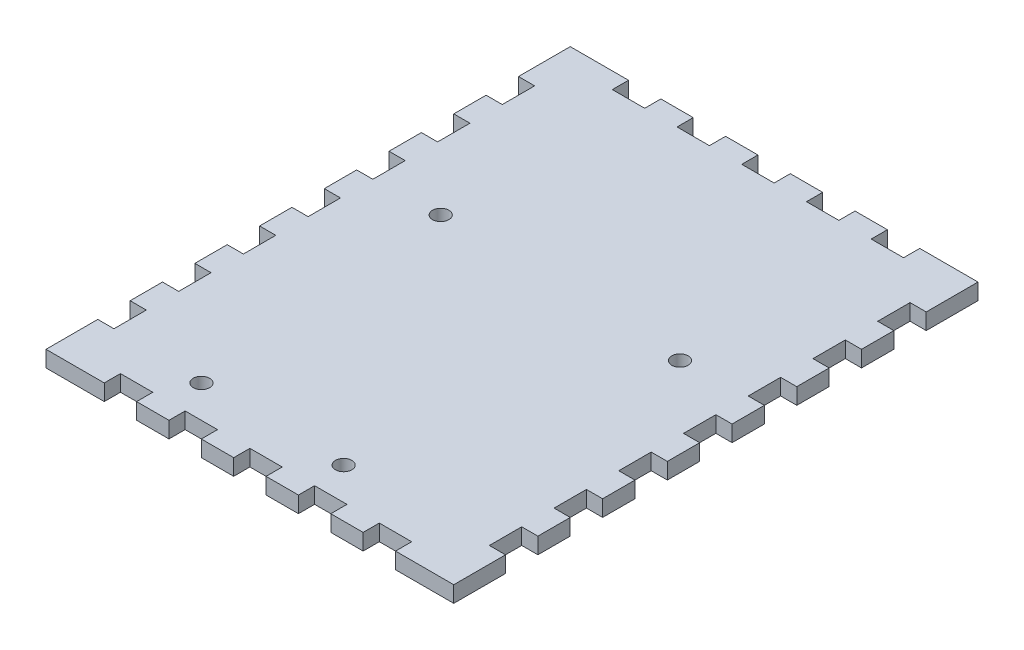
SolidWorks part; units mm, degrees
material "Acrylic (Medium-high impact)"
ref_plane "Front Plane" through (0, 0, 0) normal (0, 0, 1) x (1, 0, 0)
ref_plane "Top Plane" through (0, 0, 0) normal (0, 1, 0) x (1, 0, 0)
ref_plane "Right Plane" through (0, 0, 0) normal (1, 0, 0) x (0, 0, -1)
sketch "Sketch1" plane through (0, 0, 0) normal (0, 1, 0) x (1, 0, 0)
  line L1 (-40.005, 51.435) -> (40.005, 51.435)
  line L2 (-40.005, 51.435) -> (-40.005, -51.435)
  line L3 (-40.005, -51.435) -> (40.005, -51.435)
  line L4 (40.005, 51.435) -> (40.005, -51.435)
  line L5 (-40.005, 51.435) -> (40.005, -51.435) construction
  line L6 (-40.005, -51.435) -> (40.005, 51.435) construction
  point P0 (0, 0)
  dimension "D1" = 102.87
  dimension "D2" = 80.01
extrude "Boss-Extrude1" add sketch "Sketch1" along normal blind 3.175
sketch "Sketch2" plane through (0, 3.175, 0) normal (0, 1, 0) x (1, 0, 0)
  line L0 (-40.005, -41.275) -> (-36.83, -41.275)
  line L1 (-40.005, 51.435) -> (-40.005, -51.435) construction
  line L2 (-36.83, -41.275) -> (-36.83, -34.925)
  line L3 (-36.83, -34.925) -> (-40.005, -34.925)
  line L4 (-40.005, -51.435) -> (40.005, -51.435) construction
  line L5 (-40.005, -28.575) -> (-36.83, -28.575)
  line L6 (-40.005, 51.435) -> (-40.005, -51.435) construction
  line L7 (-36.83, -28.575) -> (-36.83, -22.225)
  line L8 (-36.83, -22.225) -> (-40.005, -22.225)
  line L9 (-40.005, -15.875) -> (-36.83, -15.875)
  line L10 (-36.83, -15.875) -> (-36.83, -9.525)
  line L11 (-36.83, -9.525) -> (-40.005, -9.525)
  line L12 (-40.005, -3.175) -> (-36.83, -3.175)
  line L13 (-36.83, -3.175) -> (-36.83, 3.175)
  line L14 (-36.83, 3.175) -> (-40.005, 3.175)
  line L15 (-40.005, 9.525) -> (-36.83, 9.525)
  line L16 (-36.83, 9.525) -> (-36.83, 15.875)
  line L17 (-36.83, 15.875) -> (-40.005, 15.875)
  line L18 (-40.005, 22.225) -> (-36.83, 22.225)
  line L19 (-36.83, 22.225) -> (-36.83, 28.575)
  line L20 (-36.83, 28.575) -> (-40.005, 28.575)
  line L21 (40.005, 51.435) -> (-40.005, 51.435) construction
  line L22 (-40.005, 51.435) -> (-40.005, -51.435) construction
  line L23 (-40.005, -34.925) -> (-40.005, -41.275)
  line L24 (-40.005, -22.225) -> (-40.005, -28.575)
  line L25 (-40.005, -9.525) -> (-40.005, -15.875)
  line L26 (-40.005, -3.175) -> (-40.005, 3.175)
  line L27 (-40.005, 15.875) -> (-40.005, 9.525)
  line L28 (-40.005, 28.575) -> (-40.005, 22.225)
  line L29 (0, 51.435) -> (0, -51.435) construction
  line L30 (40.005, 28.575) -> (40.005, 22.225)
  line L31 (40.005, 15.875) -> (40.005, 9.525)
  line L32 (40.005, -3.175) -> (40.005, 3.175)
  line L33 (40.005, -9.525) -> (40.005, -15.875)
  line L34 (40.005, -22.225) -> (40.005, -28.575)
  line L35 (40.005, -34.925) -> (40.005, -41.275)
  line L36 (36.83, 28.575) -> (40.005, 28.575)
  line L37 (36.83, 22.225) -> (36.83, 28.575)
  line L38 (40.005, 22.225) -> (36.83, 22.225)
  line L39 (36.83, 15.875) -> (40.005, 15.875)
  line L40 (36.83, 9.525) -> (36.83, 15.875)
  line L41 (40.005, 9.525) -> (36.83, 9.525)
  line L42 (36.83, 3.175) -> (40.005, 3.175)
  line L43 (36.83, -3.175) -> (36.83, 3.175)
  line L44 (40.005, -3.175) -> (36.83, -3.175)
  line L45 (36.83, -9.525) -> (40.005, -9.525)
  line L46 (36.83, -15.875) -> (36.83, -9.525)
  line L47 (40.005, -15.875) -> (36.83, -15.875)
  line L48 (36.83, -22.225) -> (40.005, -22.225)
  line L49 (36.83, -28.575) -> (36.83, -22.225)
  line L50 (40.005, -28.575) -> (36.83, -28.575)
  line L51 (36.83, -34.925) -> (40.005, -34.925)
  line L52 (36.83, -41.275) -> (36.83, -34.925)
  line L53 (40.005, -41.275) -> (36.83, -41.275)
  line L54 (-40.005, 34.925) -> (-36.83, 34.925)
  line L55 (-36.83, 34.925) -> (-36.83, 41.275)
  line L56 (-36.83, 41.275) -> (-40.005, 41.275)
  line L57 (-40.005, 41.275) -> (-40.005, 34.925)
  line L58 (40.005, 41.275) -> (40.005, 34.925)
  line L59 (36.83, 41.275) -> (40.005, 41.275)
  line L60 (36.83, 34.925) -> (36.83, 41.275)
  line L61 (40.005, 34.925) -> (36.83, 34.925)
  dimension "D1" = 3.175
  dimension "D2" = 6.35
  dimension "D3" = 10.16
  dimension "D4" = 6.35
  dimension "D5" = 6.35
  dimension "D6" = 6.35
  dimension "D7" = 6.35
  dimension "D8" = 6.35
  dimension "D9" = 10.16
  dimension "D10" = 6.35
extrude "Cut-Extrude1" cut sketch "Sketch2" against normal through all
sketch "Sketch3" plane through (0, 3.175, 0) normal (0, 1, 0) x (1, 0, 0)
  line L0 (28.575, 51.435) -> (28.575, 48.26)
  line L1 (40.005, 51.435) -> (-40.005, 51.435) construction
  line L2 (28.575, 48.26) -> (22.225, 48.26)
  line L3 (22.225, 48.26) -> (22.225, 51.435)
  line L4 (22.225, 51.435) -> (28.575, 51.435)
  line L5 (15.875, 51.435) -> (15.875, 48.26)
  line L6 (15.875, 48.26) -> (9.525, 48.26)
  line L7 (9.525, 48.26) -> (9.525, 51.435)
  line L8 (9.525, 51.435) -> (15.875, 51.435)
  line L9 (3.175, 51.435) -> (3.175, 48.26)
  line L10 (3.175, 48.26) -> (-3.175, 48.26)
  line L11 (-3.175, 48.26) -> (-3.175, 51.435)
  line L12 (-3.175, 51.435) -> (3.175, 51.435)
  line L13 (-9.525, 51.435) -> (-9.525, 48.26)
  line L14 (-9.525, 48.26) -> (-15.875, 48.26)
  line L15 (-15.875, 48.26) -> (-15.875, 51.435)
  line L16 (-15.875, 51.435) -> (-9.525, 51.435)
  line L17 (-40.005, 51.435) -> (-40.005, 41.275) construction
  line L18 (-36.83, 0) -> (36.83, 0) construction
  line L21 (-15.875, -51.435) -> (-9.525, -51.435)
  line L22 (-15.875, -48.26) -> (-15.875, -51.435)
  line L23 (-9.525, -48.26) -> (-15.875, -48.26)
  line L24 (-9.525, -51.435) -> (-9.525, -48.26)
  line L25 (40.005, 28.575) -> (40.005, 34.925) construction
  line L26 (-3.175, -51.435) -> (3.175, -51.435)
  line L27 (-3.175, -48.26) -> (-3.175, -51.435)
  line L28 (3.175, -48.26) -> (-3.175, -48.26)
  line L29 (3.175, -51.435) -> (3.175, -48.26)
  line L30 (9.525, -51.435) -> (15.875, -51.435)
  line L31 (9.525, -48.26) -> (9.525, -51.435)
  line L32 (15.875, -48.26) -> (9.525, -48.26)
  line L33 (15.875, -51.435) -> (15.875, -48.26)
  line L34 (22.225, -51.435) -> (28.575, -51.435)
  line L35 (22.225, -48.26) -> (22.225, -51.435)
  line L36 (28.575, -48.26) -> (22.225, -48.26)
  line L37 (28.575, -51.435) -> (28.575, -48.26)
  line L38 (36.83, 3.175) -> (36.83, -3.175) construction
  line L39 (-36.83, -3.175) -> (-36.83, 3.175) construction
  line L40 (-28.575, -51.435) -> (-22.225, -51.435)
  line L41 (-28.575, -48.26) -> (-28.575, -51.435)
  line L42 (-22.225, -48.26) -> (-28.575, -48.26)
  line L43 (-22.225, -51.435) -> (-22.225, -48.26)
  line L44 (-40.005, -51.435) -> (40.005, -51.435) construction
  line L45 (-22.225, 51.435) -> (-22.225, 48.26)
  line L46 (-22.225, 48.26) -> (-28.575, 48.26)
  line L47 (-28.575, 48.26) -> (-28.575, 51.435)
  line L48 (-28.575, 51.435) -> (-22.225, 51.435)
  dimension "D1" = 3.175
  dimension "D2" = 6.35
  dimension "D3" = 11.43
  dimension "D4" = 6.35
  dimension "D5" = 6.35
  dimension "D6" = 6.35
  dimension "D7" = 11.43
  dimension "D8" = 6.35
extrude "Cut-Extrude2" cut sketch "Sketch3" against normal through all
sketch "Sketch8" plane through (-2.4038, 3.175, 1.8552) normal (0, 1, 0) x (0, 0, 1)
  line L0 (46.4048, 18.2788) -> (46.4048, 11.9288) construction
  line L2 (-17.7302, 39.2338) -> (-11.3802, 39.2338) construction
  line L3 (-24.0802, -34.4262) -> (-30.4302, -34.4262) construction
  line L4 (-11.9756, -21.7071) -> (-11.9756, -34.4262) construction
  line L5 (-10.7061, 26.5147) -> (-10.7061, 39.2338) construction
  line L9 (-43.1302, -34.4262) -> (39.4198, -34.4262) construction
  line L10 (-36.7802, -34.4262) -> (-43.1302, -34.4262) construction
  line L11 (-30.4302, 39.2338) -> (-24.0802, 39.2338) construction
  circle A0 centre (-10.7061, 26.5147) radius 1.6081
  circle A1 centre (-11.9756, -21.7071) radius 1.6081
  circle A2 centre (40.0548, -16.6289) radius 1.6081
  circle A3 centre (40.0548, 11.2801) radius 1.6081
  dimension "D1" = 3.2162
  dimension "D2" = 3.2162
  dimension "D3" = 3.2162
  dimension "D4" = 3.2162
  dimension "D5" = 27.909
  dimension "D6" = 15.2346
  dimension "D7" = 52.0304
  dimension "D8" = 6.35
  dimension "D9" = 50.7609
  dimension "D10" = 48.2218
  dimension "D11" = 5.0782
  dimension "D12" = 12.7191
  dimension "D13" = 12.7191
extrude "Cut-Extrude3" cut sketch "Sketch8" against normal through all
